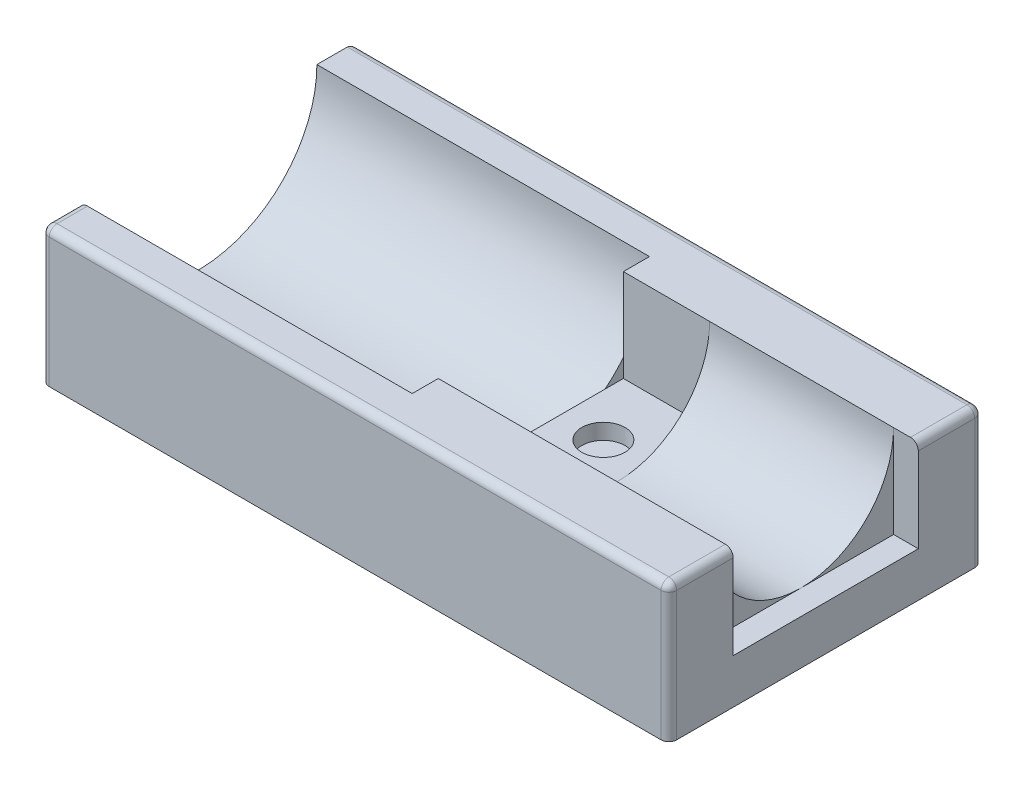
SolidWorks part; units mm, degrees
material "ABS"
ref_plane "Front Plane" through (0, 0, 0) normal (0, 0, 1) x (1, 0, 0)
ref_plane "Top Plane" through (0, 0, 0) normal (0, 1, 0) x (1, 0, 0)
ref_plane "Right Plane" through (0, 0, 0) normal (1, 0, 0) x (0, 0, -1)
sketch "Sketch1" plane through (0, 0, 0) normal (0, 1, 0) x (1, 0, 0)
  line L1 (0, 0) -> (203.2, 0)
  line L2 (0, 0) -> (0, -101.6)
  line L3 (0, -101.6) -> (203.2, -101.6)
  line L4 (203.2, 0) -> (203.2, -101.6)
  dimension "D1" = 101.6
  dimension "D2" = 203.2
extrude "Boss-Extrude1" add sketch "Sketch1" along normal blind 88.9
sketch "Sketch2" plane through (203.2, 0, 0) normal (1, 0, 0) x (0, 0, -1)
  line L0 (-101.6, 88.9) -> (0, 88.9) construction
  circle A0 centre (-50.8, 88.9) radius 29.972
  dimension "D2" = 59.944
  dimension "D1" = 50.8
extrude "Cut-Extrude1" cut sketch "Sketch2" against normal blind 203.2
sketch "Sketch3" plane through (203.2, 0, 0) normal (1, 0, 0) x (0, 0, -1)
  line L1 (-20.828, 118.872) -> (-80.772, 118.872)
  line L2 (-20.828, 118.872) -> (-20.828, 58.928)
  line L3 (-20.828, 58.928) -> (-80.772, 58.928)
  line L4 (-80.772, 118.872) -> (-80.772, 58.928)
  line L5 (-20.828, 118.872) -> (-80.772, 58.928) construction
  line L6 (-20.828, 58.928) -> (-80.772, 118.872) construction
  point P0 (-50.8, 88.9)
  dimension "D1" = 29.972
  dimension "D2" = 29.972
extrude "Cut-Extrude2" cut sketch "Sketch3" against normal blind 8.001
ref_plane "Plane1" through (135.636, 0, 0) normal (1, 0, 0) x (0, 0, -1)
sketch "Sketch4" plane through (135.636, 0, 0) normal (1, 0, 0) x (0, 0, -1)
  line L1 (-80.772, 58.928) -> (-20.828, 58.928)
  line L2 (-80.772, 58.928) -> (-80.772, 88.9)
  line L3 (-80.772, 88.9) -> (-20.828, 88.9)
  line L4 (-20.828, 58.928) -> (-20.828, 88.9)
extrude "Cut-Extrude3" cut sketch "Sketch4" against normal blind 27.94
sketch "Sketch5" plane through (0, 0, 0) normal (-1, 0, 0) x (0, 0, 1)
  line L0 (0, 88.9) -> (20.828, 88.9) construction
  circle A0 centre (50.8, 88.9) radius 38.4175
  dimension "D3" = 76.835
  dimension "D1" = 0
  dimension "D2" = 50.8
extrude "Cut-Extrude4" cut sketch "Sketch5" against normal blind 107.696
sketch "Sketch6" plane through (0, 58.928, 0) normal (0, 1, 0) x (1, 0, 0)
  line L0 (135.636, -50.8) -> (107.696, -50.8) construction
  line L1 (107.696, -74.833) -> (107.696, -26.767) construction
  line L2 (121.666, -50.8) -> (121.666, -31.75)
  circle A0 centre (121.666, -41.275) radius 6.985
  dimension "D2" = 13.97
  dimension "D1" = 19.05
extrude "Cut-Extrude5" cut sketch "Sketch6" against normal blind 5.08 contours L2 A0 | L2 A0
sketch "Sketch7" plane through (0, 0, 101.6) normal (0, 0, 1) x (1, 0, 0)
  line L0 (203.2, 88.9) -> (203.2, 0) construction
  line L1 (0, 0) -> (203.2, 0)
  line L2 (0, 0) -> (0, 6.35)
  line L3 (0, 6.35) -> (203.2, 6.35)
  line L4 (203.2, 0) -> (203.2, 6.35)
  dimension "D1" = 6.35
extrude "Boss-Extrude2" add sketch "Sketch7" along normal blind 38.1
fillet "Fillet1" radius 2.54 12 edges at (101.6, 6.35, 101.6) (0, 6.35, 120.65) (203.2, 6.35, 120.65) (0, 44.45, 0) (0, 88.9, 95.4087) (0, 47.625, 101.6) (101.6, 88.9, 0) (203.2, 44.45, 0) (203.2, 88.9, 10.414) (203.2, 88.9, 91.186) (101.6, 88.9, 101.6) (203.2, 47.625, 101.6)
sketch "Sketch8" plane through (0, 0, 0) normal (0, -1, 0) x (1, 0, 0)
  line L1 (0, 139.7) -> (203.2, 139.7)
  line L2 (0, 139.7) -> (0, 0)
  line L3 (0, 0) -> (203.2, 0)
  line L4 (203.2, 139.7) -> (203.2, 0)
  dimension "D1" = 203.2
  dimension "D2" = 139.7
extrude "Cut-Extrude6" cut sketch "Sketch8" against normal blind 44.45
